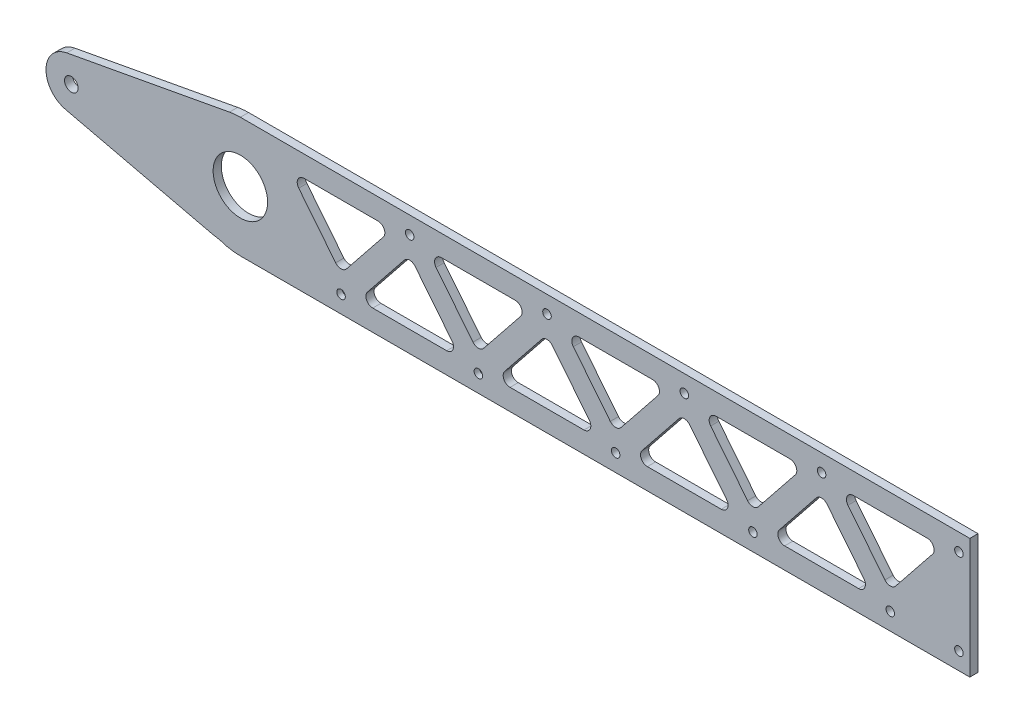
SolidWorks part; units mm, degrees
material "6061-T6 (SS)"
ref_plane "Front" through (0, 0, 0) normal (0, 0, 1) x (1, 0, 0)
ref_plane "Top" through (0, 0, 0) normal (0, 1, 0) x (1, 0, 0)
ref_plane "Right" through (0, 0, 0) normal (1, 0, 0) x (0, 0, -1)
sketch "Sketch1" plane through (0, 0, 0) normal (0, 0, 1) x (1, 0, 0)
  line L0 (-212.5, 35) -> (212.5, 35)
  line L1 (-212.5, -35) -> (212.5, -35)
  line L2 (-212.5, 0) -> (212.5, 0) construction
  line L3 (-212.5, 35) -> (-325.7529, 54.9695)
  line L4 (-325.7529, 54.9695) -> (-325.7529, -15.0305)
  line L5 (-325.7529, -15.0305) -> (-212.5, -35)
  line L6 (-212.5, 35) -> (-212.5, -35) construction
  line L7 (-310.9808, 52.3648) -> (-310.9808, -17.6352) construction
  line L8 (212.5, 35) -> (212.5, -35)
  line L9 (-313.6661, 16.8908) -> (-218.8625, 34.4168)
  line L10 (-314.3603, -12.0155) -> (-228.7491, -32.1348)
  arc A0 (-212.5, 35) -> (-212.5, -35) centre (-212.5, 0) ccw
  circle A2 centre (-212.5, 0) radius 15.875
  circle A4 centre (-310.9808, 2.3648) radius 3.9688
  arc A5 (-310.9808, 17.1369) -> (-310.9808, -12.4073) centre (-310.9808, 2.3648) ccw
  point P6 (0, 0)
  point P12 (-325.7529, 19.9695)
  point P17 (-310.9808, 17.3648)
  dimension "D2" = 35
  dimension "D3" = 31.75
  dimension "D7" = 7.9375
  dimension "D1" = 425
  dimension "D5" = 100
  dimension "D6" = 115
  dimension "D8" = 100
  dimension "D9" = 20
extrude "Boss-Extrude1" add sketch "Sketch1" along normal blind 4.7625
sketch "Sketch6" plane through (0, 0, 0) normal (0, 0, -1) x (-1, 0, 0)
  line L0 (-166.15, 35) -> (-166.15, -35) construction
  line L1 (212.5, 35) -> (-212.5, 35) construction
  line L2 (212.5, -35) -> (-212.5, -35) construction
  line L3 (-212.5, 35) -> (-212.5, -35) construction
  circle A0 centre (212.5, 0) radius 50 construction
  dimension "D2" = 100
  dimension "D1" = 46.35
hole_wizard "#10 Clearance Hole1" positions "Sketch4" profile "Sketch5" hole size "#10" standard "ANSI Inch" end condition through all
sketch "Sketch4" plane through (0, 0, 0) normal (0, 0, -1) x (-1, 0, 0)
  line L0 (212.5, 35) -> (-212.5, 35) construction
  line L1 (212.5, -35) -> (-212.5, -35) construction
  line L2 (-166.15, 35) -> (-166.15, -35) construction
  point P4 (-126.15, 25)
  point P6 (-86.15, -25)
  dimension "D1" = 10
  dimension "D2" = 10
  dimension "D3" = 40
  dimension "D4" = 40
sketch "Sketch5" plane through (126.15, 25, 0) normal (1, 0, 0) x (0, 1, 0)
  line L0 (0, 0) -> (0, 4.7625)
  line L1 (0, 4.7625) -> (2.4892, 4.7625)
  line L2 (2.4892, 4.7625) -> (2.4892, 0)
  line L5 (2.4892, 0) -> (0, 0)
  line L11 (0, -6.35) -> (0, 107.95) construction
  dimension "Thru Hole Dia." = 4.9784
  dimension "Thru Hole Depth" = 4.7625
sketch "Sketch7" plane through (0, 0, 0) normal (0, 0, -1) x (-1, 0, 0)
pattern_linear "LPattern1" count 4 spacing 80 along (-1, 0, 0) of "#10 Clearance Hole1"
sketch "Sketch13" plane through (0, 0, 0) normal (0, 0, -1) x (-1, 0, 0)
  line L6 (-46.15, 25) -> (-86.15, -25) construction
  line L7 (-126.15, 25) -> (-86.15, -25) construction
  line L8 (-86.15, -14.5949) -> (-115.9987, 22.716)
  line L9 (-115.9987, 22.716) -> (-56.3013, 22.716)
  line L10 (-56.3013, 22.716) -> (-86.15, -14.5949)
  line L11 (-75.9987, -22.716) -> (-46.15, 14.5949)
  line L12 (-46.15, 14.5949) -> (-16.3013, -22.716)
  line L13 (-16.3013, -22.716) -> (-75.9987, -22.716)
  line L14 (-46.15, 25) -> (-6.15, -25) construction
  line L15 (-56.3013, 22.716) -> (-46.15, 14.5949) construction
  line L16 (-46.15, 14.5949) -> (-35.9987, 22.716) construction
  line L17 (-86.15, -14.5949) -> (-96.3013, -22.716) construction
  circle A0 centre (-6.15, -25) radius 2.4892 construction
  circle A1 centre (-46.15, 25) radius 2.4892 construction
  circle A2 centre (-86.15, -25) radius 2.4892 construction
  circle A3 centre (-126.15, 25) radius 2.4892 construction
  circle A4 centre (-6.15, -25) radius 2.4892
  circle A5 centre (-46.15, 25) radius 2.4892
  circle A6 centre (-86.15, -25) radius 2.4892
  circle A7 centre (-126.15, 25) radius 2.4892
  point P18 (-51.2256, 18.6554)
  point P19 (-41.0744, 18.6554)
  point P20 (-91.2256, -18.6554)
  dimension "D1" = 13
extrude "Cut-Extrude1" cut sketch "Sketch13" against normal blind 10 contours L10 L9 L8
fillet "Fillet1" radius 4 3 edges at (86.15, -14.5949, 2.3813) (56.3013, 22.716, 2.3813) (115.9987, 22.716, 2.3813)
sketch "Sketch14" plane through (0, 0, 0) normal (0, 0, -1) x (-1, 0, 0)
  line L1 (-61.5003, 16.2172) -> (-83.0265, -10.6906) construction
  line L2 (-56.3013, 22.716) -> (-86.15, -14.5949) construction
  line L3 (-46.15, 25) -> (-86.15, -25) construction
  line L4 (-46.15, 14.5949) -> (-75.9987, -22.716)
  line L5 (-75.9987, -22.716) -> (-16.3013, -22.716)
  line L6 (-16.3013, -22.716) -> (-46.15, 14.5949)
  line L7 (-89.2735, -10.6906) -> (-110.7997, 16.2172) construction
  line L8 (-86.15, -14.5949) -> (-110.7997, 16.2172) construction
  line L9 (-56.3013, 22.716) -> (-46.15, 14.5949) construction
  line L10 (-107.6762, 22.716) -> (-64.6238, 22.716) construction
  line L11 (-107.6762, 22.716) -> (-56.3013, 22.716) construction
  circle A0 centre (-6.15, -25) radius 2.4892 construction
  circle A1 centre (-86.15, -25) radius 2.4892 construction
  circle A2 centre (-46.15, 25) radius 2.4892 construction
  circle A3 centre (-6.15, -25) radius 2.4892
  circle A4 centre (-86.15, -25) radius 2.4892
  circle A5 centre (-46.15, 25) radius 2.4892
  point P16 (-51.2256, 18.6554)
extrude "Cut-Extrude2" cut sketch "Sketch14" against normal through all contours L4 L5 L6
fillet "Fillet2" radius 4 3 edges at (75.9987, -22.716, 2.3813) (16.3013, -22.716, 2.3813) (46.15, 14.5949, 2.3813)
pattern_linear "LPattern2" count 4 spacing 80 along (-1, 0, 0) of "Cut-Extrude1", "Fillet1"
pattern_linear "LPattern3" count 3 spacing 80 along (-1, 0, 0) of "Cut-Extrude2", "Fillet2"
pattern_linear "LPattern4" count 2 spacing 80 along (1, 0, 0) of "Cut-Extrude2", "Fillet2"
pattern_linear "LPattern5" count 2 spacing 80 along (1, 0, 0) of "Cut-Extrude1", "Fillet1"
sketch "Sketch15" plane through (0, 0, 4.7625) normal (0, 0, 1) x (1, 0, 0)
  line L0 (126.15, 25) -> (206.15, 25) construction
  line L1 (206.15, 25) -> (166.15, -25) construction
  line L2 (166.15, -25) -> (86.15, -25) construction
  line L3 (166.15, 35) -> (166.15, -35) construction
  line L4 (206.15, 25) -> (206.15, -25) construction
  point P3 (206.15, -25)
  point P7 (166.15, -25)
  point P13 (206.15, 25)
hole_wizard "#10 Clearance Hole2" positions "Sketch16" profile "Sketch17" hole size "#10" standard "ANSI Inch" end condition up to next
sketch "Sketch16" plane through (0, 0, 4.7625) normal (0, 0, 1) x (1, 0, 0)
  point P0 (206.15, 25)
  point P3 (206.15, -25)
  point P6 (166.15, -25)
sketch "Sketch17" plane through (206.15, 25, 4.7625) normal (1, 0, 0) x (0, -1, 0)
  line L0 (0, 0) -> (0, 4.7625)
  line L1 (0, 4.7625) -> (2.4892, 4.7625)
  line L2 (2.4892, 4.7625) -> (2.4892, 0)
  line L5 (2.4892, 0) -> (0, 0)
  line L11 (0, -6.35) -> (0, 107.95) construction
  dimension "Thru Hole Dia." = 4.9784
  dimension "Thru Hole Depth" = 4.7625
hole_wizard "CBORE for #10 Button Head Cap Screw1" positions "Sketch18" profile "Sketch21" counterbore size "#10" standard "ANSI Inch" end condition through all
sketch "Sketch18" plane through (0, 0, 0) normal (0, 0, -1) x (-1, 0, 0)
  point P13 (153.85, -25)
  point P16 (73.85, -25)
sketch "Sketch21" plane through (-153.85, -25, 0) normal (1, 0, 0) x (0, 1, 0)
  line L0 (0, 0) -> (0, 4.7625)
  line L1 (0, 4.7625) -> (2.4892, 4.7625)
  line L3 (2.4892, 4.7625) -> (2.4892, 1.5875)
  line L4 (2.4892, 1.5875) -> (3.175, 1.5875)
  line L5 (3.175, 1.5875) -> (3.175, 0)
  line L7 (3.175, 0) -> (0, 0)
  line L11 (0, -6.35) -> (0, 107.95) construction
  dimension "Thru Hole Dia." = 4.9784
  dimension "Thru Hole Depth" = 4.7625
  dimension "C'Bore Dia." = 6.35
  dimension "C'Bore Depth" = 1.5875
